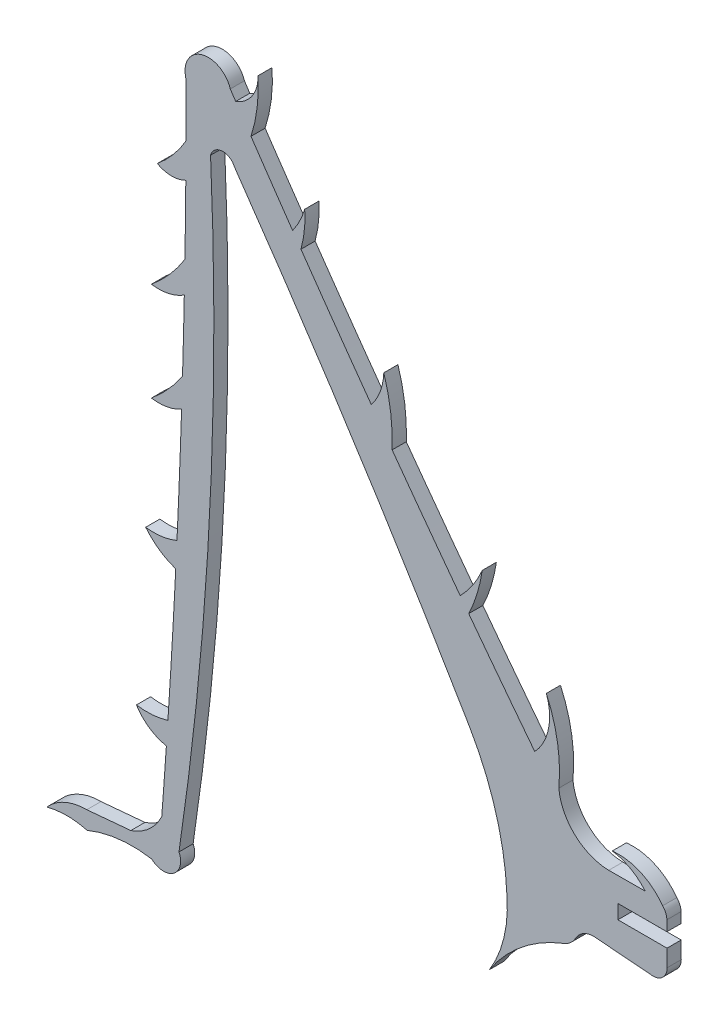
SolidWorks part; units mm, degrees
ref_plane "Front Plane" through (0, 0, 0) normal (0, 0, 1) x (1, 0, 0)
ref_plane "Top Plane" through (0, 0, 0) normal (0, 1, 0) x (1, 0, 0)
ref_plane "Right Plane" through (0, 0, 0) normal (1, 0, 0) x (0, 0, -1)
sketch "Sketch1" plane through (0, 0, 0) normal (0, 0, 1) x (1, 0, 0)
  line L0 (-29.1074, -37.9034) -> (-24.3646, -37.4772)
  line L1 (27.1317, -15.4356) -> (31.0692, -15.4119)
  line L2 (33.3982, -16.9255) -> (33.4062, -18.0358)
  line L3 (33.4062, -18.0358) -> (28.1109, -18.0358)
  line L4 (28.1109, -18.0358) -> (28.1228, -19.5618)
  line L5 (28.1228, -19.5618) -> (33.4141, -19.5608)
  line L6 (33.4141, -19.5608) -> (33.426, -21.3888)
  line L7 (31.9122, -22.9257) -> (25.5199, -22.4081)
  arc A0 (-24.3646, -37.4772) -> (-21.0334, -34.5134) centre (-26.1926, -32.0685) ccw
  arc A1 (-21.0334, -34.5134) -> (-20.5351, -27.6622) centre (-918.9597, 34.2391) ccw
  arc A2 (-20.3687, -25.1986) -> (-19.5238, -10.6354) centre (-918.9597, 34.2391) ccw
  arc A3 (-19.3924, -7.9186) -> (-18.8938, 4.5759) centre (-918.9597, 34.2391) ccw
  arc A4 (-18.7959, 7.7124) -> (-18.6027, 15.375) centre (-918.9597, 34.2391) ccw
  arc A5 (-18.5385, 18.7388) -> (-18.4413, 26.1693) centre (-918.9597, 34.2391) ccw
  arc A6 (-18.4157, 29.8603) -> (-18.4057, 35.2839) centre (-918.9597, 34.2391) ccw
  arc A7 (-13.6486, 37.0887) -> (-13.0631, 36.2178) centre (663.7396, 491.8226) ccw
  arc A8 (-11.4179, 33.7833) -> (-6.9326, 27.2406) centre (663.7396, 491.8226) ccw
  arc A9 (-6.0305, 25.941) -> (1.5487, 15.2296) centre (663.7396, 491.8226) ccw
  arc A10 (3.7932, 12.1265) -> (11.1302, 2.1915) centre (663.7396, 491.8226) ccw
  arc A11 (12.0467, 0.9724) -> (19.1648, -8.3384) centre (663.7396, 491.8226) ccw
  arc A12 (21.7528, -10.4648) -> (27.1317, -15.4356) centre (27.2476, -9.9145) ccw
  arc A13 (33.3982, -16.9255) -> (32.9447, -15.8481) centre (31.8712, -16.934) ccw
  arc A14 (31.9122, -22.9257) -> (33.426, -21.3888) centre (31.9011, -21.4007) ccw
  arc A15 (25.5199, -22.4081) -> (23.5753, -23.5513) centre (25.514, -24.6235) ccw
  arc A17 (16.1685, -23.3144) -> (12.1174, -9.511) centre (-13.6444, -24.5677) ccw
  arc A18 (12.1174, -9.511) -> (-13.1921, 30.0279) centre (-487.6056, -301.5231) ccw
  arc A19 (-13.1921, 30.0279) -> (-15.7729, 29.8433) centre (-14.4506, 29.4892) ccw
  arc A20 (-19.1754, -36.8788) -> (-15.7729, 29.8433) centre (-362.5277, 14.0785) ccw
  arc A21 (32.9447, -15.8481) -> (27.5143, -13.442) centre (28.1951, -19.2364) ccw
  arc A22 (31.0692, -15.4119) -> (27.5143, -13.442) centre (26.7073, -19.0908) ccw
  arc A23 (22.2675, -24.6915) -> (14.0374, -31.5209) centre (28.3142, -40.3519) ccw
  arc A24 (22.2675, -24.6915) -> (23.5753, -23.5513) centre (21.3526, -22.322) ccw
  arc A25 (14.0374, -31.5209) -> (16.1685, -23.3144) centre (3.15, -24.3138) ccw
  arc A26 (21.7528, -10.4648) -> (20.4111, -2.2874) centre (5.8121, -8.8815) ccw
  arc A27 (19.1648, -8.3384) -> (20.4111, -2.2874) centre (14.8841, -4.3029) ccw
  arc A28 (12.0467, 0.9724) -> (13.5027, 5.7365) centre (-2.7782, 8.108) ccw
  arc A29 (11.1302, 2.1915) -> (13.5027, 5.7365) centre (2.8873, 10.2746) ccw
  arc A30 (3.7932, 12.1265) -> (2.8989, 18.8784) centre (-15.9477, 12.9471) ccw
  arc A31 (-6.0305, 25.941) -> (-5.6252, 29.8783) centre (-17.3417, 29.0948) ccw
  arc A32 (-6.9326, 27.2406) -> (-5.6252, 29.8783) centre (-13.6503, 32.213) ccw
  arc A33 (-13.6486, 37.0887) -> (-18.4649, 35.826) centre (-16.0313, 36.3605) ccw
  arc A34 (-18.4057, 35.2839) -> (-18.4649, 35.826) centre (-20.9457, 35.281) ccw
  arc A35 (-11.4179, 33.7833) -> (-10.665, 39.8154) centre (-26.831, 38.77) ccw
  arc A36 (-13.0631, 36.2178) -> (-10.665, 39.8154) centre (-14.3538, 39.6762) ccw
  arc A37 (-22.1097, -39.0106) -> (-29.0736, -39.8148) centre (-24.2028, -51.4393) ccw
  arc A38 (-22.1097, -39.0106) -> (-19.1754, -36.8788) centre (-20.8456, -37.6652) ccw
  arc A39 (-29.1074, -37.9034) -> (-33.4261, -39.8154) centre (-29.155, -43.6293) ccw
  arc A40 (-29.0736, -39.8148) -> (-33.4261, -39.8154) centre (-31.2488, -47.7567) ccw
  arc A41 (-21.5151, 26.1969) -> (-18.4157, 29.8603) centre (-30.2009, 36.6881) ccw
  arc A42 (-21.5151, 26.1969) -> (-18.4413, 26.1693) centre (-19.9522, 29.0819) ccw
  arc A43 (-22.1516, 14.6148) -> (-18.6027, 15.375) centre (-21.3886, 19.7168) ccw
  arc A44 (-22.1516, 14.6148) -> (-18.5385, 18.7388) centre (-32.8931, 27.6703) ccw
  arc A45 (-22.1516, 3.9893) -> (-18.8938, 4.5759) centre (-21.3886, 9.0913) ccw
  arc A46 (-22.1516, 3.9893) -> (-18.7959, 7.7124) centre (-32.8931, 17.0448) ccw
  arc A47 (-22.7619, -8.3694) -> (-19.3924, -7.9186) centre (-21.8849, -2.1074) ccw
  arc A48 (-22.7619, -8.3694) -> (-19.5238, -10.6354) centre (-17.2973, -4.0071) ccw
  arc A49 (-23.7611, -25.4496) -> (-20.3687, -25.1986) centre (-22.6109, -17.9444) ccw
  arc A50 (-23.7611, -25.4496) -> (-20.5351, -27.6622) centre (-19.604, -22.8466) ccw
  arc A51 (1.5487, 15.2296) -> (2.8989, 18.8784) centre (-3.3818, 19.1283) ccw
extrude "Boss-Extrude1" add sketch "Sketch1" along normal blind 1.524 contours A51 A9 A31 A32 A8 A35 A36 A7 A33 A34 A6 A41 A42 A5 A44 A43 A4 A46 A45 A3 A47 A48 A2 A49 A50 A1 A0 L0 A39 A40 A37 A38 A20 A19 A18 A17 A25 A23 A24 A15 L7 A14 L6 L5 L4 L3 L2 A13 A21 A22 L1
